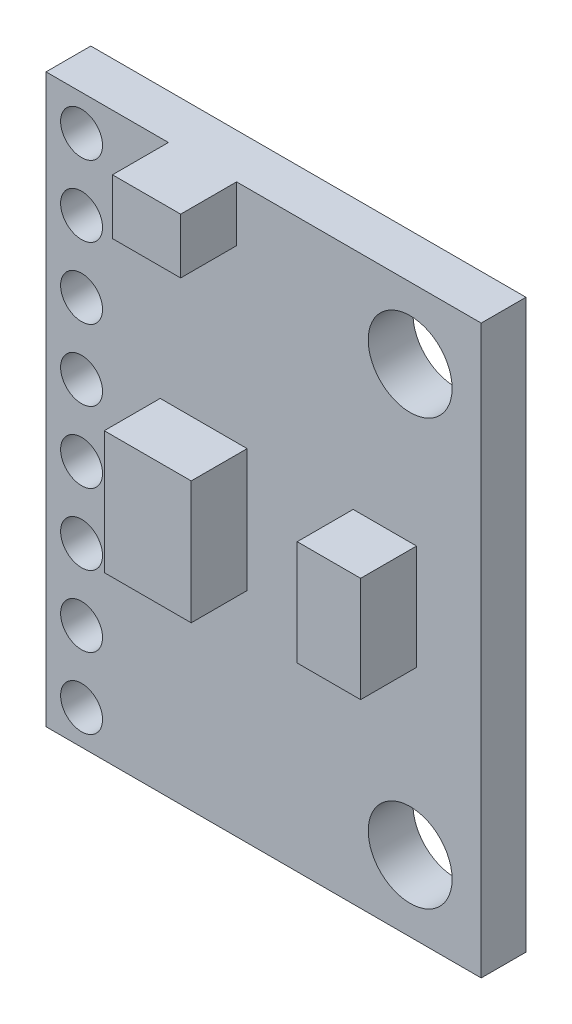
SolidWorks part; units mm, degrees
ref_plane "前视基准面" through (0, 0, 0) normal (0, 0, 1) x (1, 0, 0)
ref_plane "上视基准面" through (0, 0, 0) normal (0, 1, 0) x (1, 0, 0)
ref_plane "右视基准面" through (0, 0, 0) normal (1, 0, 0) x (0, 0, -1)
sketch "草图1" plane through (0, 0, 0) normal (0, 0, 1) x (1, 0, 0)
  line L1 (-7.78, -10.14) -> (7.78, -10.14)
  line L2 (-7.78, -10.14) -> (-7.78, 10.14)
  line L3 (-7.78, 10.14) -> (7.78, 10.14)
  line L4 (7.78, -10.14) -> (7.78, 10.14)
  line L5 (-7.78, -10.14) -> (7.78, 10.14) construction
  line L6 (-7.78, 10.14) -> (7.78, -10.14) construction
  circle A0 centre (5.24, 7.6) radius 1.5
  circle A1 centre (5.24, -7.6) radius 1.5
  circle A2 centre (-6.51, 8.87) radius 0.75
  circle A3 centre (-6.51, 6.33) radius 0.75
  circle A4 centre (-6.51, 3.79) radius 0.75
  circle A5 centre (-6.51, 1.25) radius 0.75
  circle A6 centre (-6.51, -1.29) radius 0.75
  circle A7 centre (-6.51, -3.83) radius 0.75
  circle A8 centre (-6.51, -6.37) radius 0.75
  circle A9 centre (-6.51, -8.91) radius 0.75
  point P0 (0, 0)
  dimension "D3" = 2.54
  dimension "D4" = 2.54
  dimension "D5" = 2.54
  dimension "D6" = 2.54
  dimension "D7" = 3
  dimension "D8" = 3
  dimension "D9" = 1.5
  dimension "D10" = 1.27
  dimension "D11" = 1.27
  dimension "D1" = 15.56
  dimension "D2" = 20.28
  dimension "D12" = 8
extrude "凸台-拉伸1" add sketch "草图1" along normal blind 1.6
sketch "草图2" plane through (0, 0, 1.6) normal (0, 0, 1) x (1, 0, 0)
  line L0 (7.78, 10.14) -> (-7.78, 10.14) construction
  line L1 (3.2015, -1.6766) -> (5.4686, -1.6766)
  line L2 (3.2015, -1.6766) -> (3.2015, 2.0813)
  line L3 (3.2015, 2.0813) -> (5.4686, 2.0813)
  line L4 (5.4686, -1.6766) -> (5.4686, 2.0813)
  line L5 (-3.6981, -2.3261) -> (-0.589, -2.3261)
  line L6 (-3.6981, -2.3261) -> (-3.6981, 2.0684)
  line L7 (-3.6981, 2.0684) -> (-0.589, 2.0684)
  line L8 (-0.589, -2.3261) -> (-0.589, 2.0684)
  line L9 (-3.4044, 10.14) -> (-0.9666, 10.14)
  line L10 (-3.4044, 10.14) -> (-3.4044, 8.1639)
  line L11 (-3.4044, 8.1639) -> (-0.9666, 8.1639)
  line L12 (-0.9666, 10.14) -> (-0.9666, 8.1639)
extrude "凸台-拉伸2" add sketch "草图2" along normal blind 2
